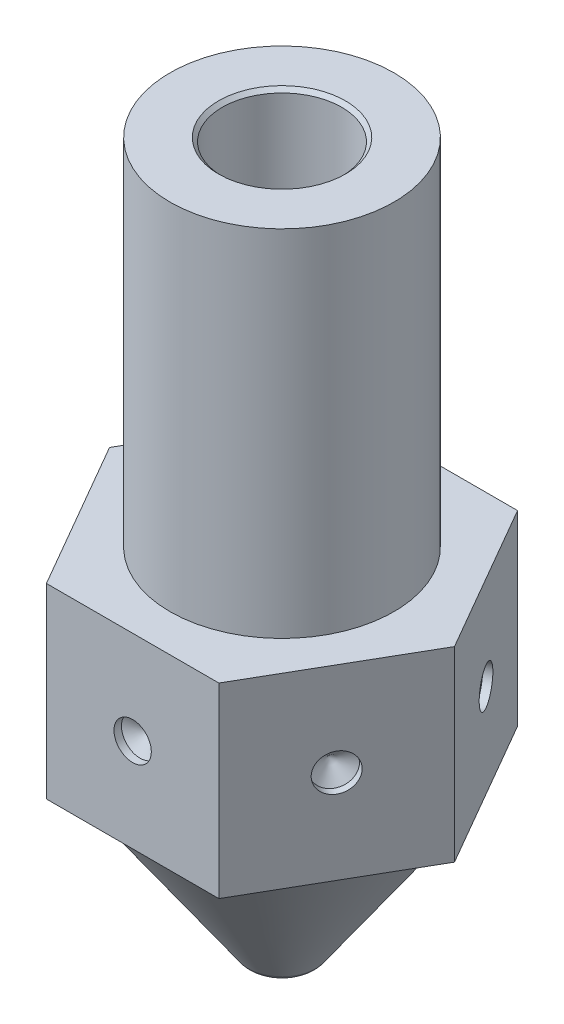
SolidWorks part; units mm, degrees
material "Latón"
ref_plane "Alzado" through (0, 0, 0) normal (0, 0, 1) x (1, 0, 0)
ref_plane "Planta" through (0, 0, 0) normal (0, 1, 0) x (1, 0, 0)
ref_plane "Vista lateral" through (0, 0, 0) normal (1, 0, 0) x (0, 0, -1)
sketch "Croquis1" plane through (0, 0, 0) normal (0, 0, 1) x (1, 0, 0)
  line L0 (0.5, 0) -> (0.575, 0)
  line L1 (0.9027, 0.1706) -> (3.9342, 4.5)
  line L2 (0.5, 2) -> (1.6, 3.571)
  line L3 (7.4352, 9.5) -> (3, 9.5)
  line L4 (3, 9.5) -> (3, 19)
  line L5 (3, 19) -> (1.6, 19)
  line L6 (1.6, 19) -> (1.6, 3.571)
  line L7 (0.5, 2) -> (0.5, 0)
  line L8 (0, 0) -> (0, 18.2336) construction
  line L11 (3.9342, 4.5) -> (6.6406, 4.5)
  line L12 (6.6406, 8.3652) -> (6.6406, 4.5)
  line L13 (6.6406, 8.3652) -> (7.4352, 9.5)
  arc A0 (0.575, 0) -> (0.9027, 0.1706) centre (0.575, 0.4) ccw
  point P14 (0.7832, 0)
  dimension "D8" = 0.075
  dimension "D2" = 0.4
  dimension "D1" = 0.5
  dimension "D3" = 1.6
  dimension "D4" = 3
  dimension "D5" = 9.5
  dimension "D6" = 9.5
  dimension "D7" = 35
  dimension "D9" = 2
  dimension "D13" = 4.5
revolve "Revolución1" add sketch "Croquis1" angle 360 about L8
cosmetic thread "Rosca cosmética1" parameters "D2"=4.891
sketch "Croquis2" plane through (0, 9.5, 0) normal (0, 1, 0) x (1, 0, 0)
  line L1 (2.3094, 4) -> (-2.3094, 4)
  line L2 (-2.3094, 4) -> (-4.6188, 0)
  line L3 (-4.6188, 0) -> (-2.3094, -4)
  line L4 (-2.3094, -4) -> (2.3094, -4)
  line L5 (2.3094, -4) -> (4.6188, 0)
  line L6 (4.6188, 0) -> (2.3094, 4)
  circle A0 centre (0, 0) radius 4 construction
  circle A2 centre (0, 0) radius 7.4352 construction
  circle A3 centre (0, 0) radius 7.4352
  dimension "D1" = 8
extrude "Cortar-Extruir1" cut sketch "Croquis2" against normal blind 7 from offset 1
chamfer "Chaflán1" distance 0.1 angle 45 1 edges at (0, 19, -1.6)
ref_plane "Plano1" through (4.6188, 4.5, 0) normal (0, 1, 0) x (1, 0, 0)
sketch "Croquis3" plane through (0, 0, 4) normal (0, 0, 1) x (1, 0, 0)
  line L0 (-2.3094, 9.5) -> (2.3094, 4.5) construction
  point P4 (0, 7)
sketch "Croquis4" plane through (3.4641, 0, 2) normal (0.866, 0, 0.5) x (0.5, 0, -0.866)
  line L0 (-2.3094, 9.5) -> (2.3094, 4.5) construction
  point P4 (0, 7)
sketch "Croquis5" plane through (3.4641, 0, -2) normal (0.866, 0, -0.5) x (-0.5, 0, -0.866)
  line L0 (-2.3094, 9.5) -> (2.3094, 4.5) construction
  point P4 (0, 7)
sketch "Croquis6" plane through (0, 0, -4) normal (0, 0, -1) x (-1, 0, 0)
  line L0 (-2.3094, 9.5) -> (2.3094, 4.5) construction
  point P4 (0, 7)
sketch "Croquis7" plane through (-3.4641, 0, -2) normal (-0.866, 0, -0.5) x (-0.5, 0, 0.866)
  line L0 (-2.3094, 9.5) -> (2.3094, 4.5) construction
  point P4 (0, 7)
sketch "Croquis8" plane through (-3.4641, 0, 2) normal (-0.866, 0, 0.5) x (0.5, 0, 0.866)
  line L0 (-2.3094, 9.5) -> (2.3094, 4.5) construction
  point P4 (0, 7)
hole_wizard "Diámetro de taladro Ø1.0 (1)1" positions "Croquis3D1" profile "Croquis9" hole size "Ø1.0" standard "Din"
sketch3d "Croquis3D1"
  point P0 (0, 7, 4)
  point P3 (3.4641, 7, 2)
  point P6 (3.4641, 7, -2)
  point P9 (0, 7, -4)
  point P12 (-3.4641, 7, -2)
  point P15 (-3.4641, 7, 2)
sketch "Croquis9" plane through (0, 7, 4) normal (1, 0, 0) x (0, -1, 0)
  line L0 (0, 0) -> (0, 0.5004)
  line L1 (0, 0.5004) -> (0.5, 0.2)
  line L2 (0.5, 0.2) -> (0.5, 0)
  line L5 (0.5, 0) -> (0, 0)
  line L10 (0, 0.5004) -> (-0.5, 0.2) construction
  line L11 (0, -6.35) -> (0, 107.95) construction
  dimension "Diámetro de taladro" = 1
  dimension "Profundidad de taladro" = 0.2
  dimension "Ángulo de perforador" = 118
